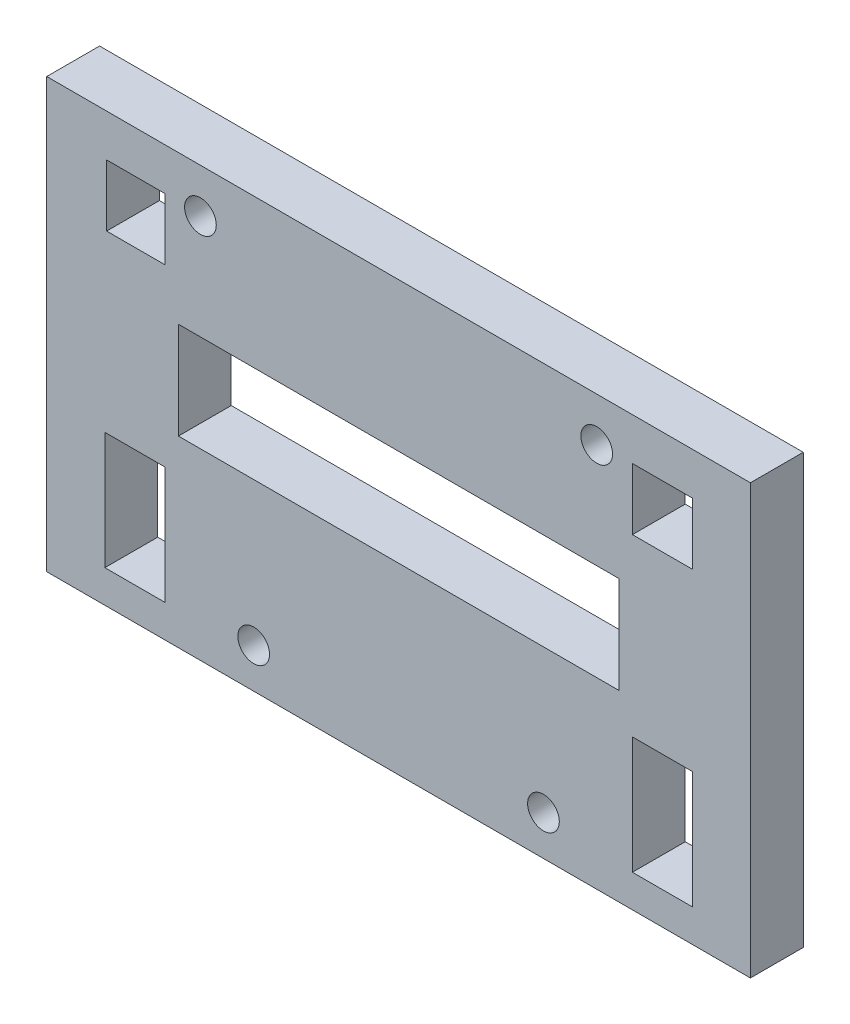
SolidWorks part; units mm, degrees
ref_plane "Plano frontal" through (0, 0, 0) normal (0, 0, 1) x (1, 0, 0)
ref_plane "Plano superior" through (0, 0, 0) normal (0, 1, 0) x (1, 0, 0)
ref_plane "Plano direito" through (0, 0, 0) normal (1, 0, 0) x (0, 0, -1)
sketch "Model" plane through (0, 0, 0) normal (0, 0, 1) x (1, 0, 0)
  line L0 (43.7166, 10.9397) -> (36.9166, 10.9397)
  line L1 (37.1166, 44.1397) -> (37.1166, 51.1397)
  line L2 (43.7166, 44.1397) -> (37.1166, 44.1397)
  line L3 (43.7166, 51.1397) -> (43.7166, 44.1397)
  line L4 (43.7166, 24.252) -> (43.7166, 10.9397)
  line L5 (36.9166, 24.252) -> (43.7166, 24.252)
  line L6 (36.9166, 10.9397) -> (36.9166, 24.252)
  line L7 (96.8166, 10.9397) -> (103.6166, 10.9397)
  line L8 (103.6166, 10.9397) -> (103.6166, 24.252)
  line L9 (103.6166, 24.252) -> (96.8166, 24.252)
  line L10 (96.8166, 24.252) -> (96.8166, 10.9397)
  line L11 (96.8166, 44.1397) -> (103.6166, 44.1397)
  line L12 (103.6166, 44.1397) -> (103.6166, 51.1397)
  line L13 (103.6166, 51.1397) -> (96.8166, 51.1397)
  line L14 (30.3166, 7.2414) -> (110.2166, 7.2414)
  line L15 (30.3166, 55.9397) -> (30.3166, 7.2414)
  line L16 (110.2166, 55.9397) -> (30.3166, 55.9397)
  line L17 (45.2666, 39.0571) -> (45.2666, 28.0571)
  line L18 (45.2666, 28.0571) -> (95.2666, 28.0571)
  line L19 (95.2666, 28.0571) -> (95.2666, 39.0571)
  line L20 (95.2666, 39.0571) -> (45.2666, 39.0571)
  line L21 (37.1166, 51.1397) -> (43.7166, 51.1397)
  line L22 (110.2166, 7.2414) -> (110.2166, 55.9397)
  line L23 (96.8166, 51.1397) -> (96.8166, 44.1397)
  circle A0 centre (53.8166, 11.7571) radius 1.8
  circle A1 centre (92.7666, 50.9397) radius 1.8
  circle A2 centre (86.7166, 11.7571) radius 1.8
  circle A3 centre (47.7666, 50.9397) radius 1.8
extrude "Ressalto-extrusão1" add sketch "Model" along normal blind 6
ref_plane "Plano1" through (70.2666, 0, 0) normal (1, 0, 0) x (0, 0, -1)
ref_plane "Plano2" through (0, 31.0397, 0) normal (0, 1, 0) x (1, 0, 0)
